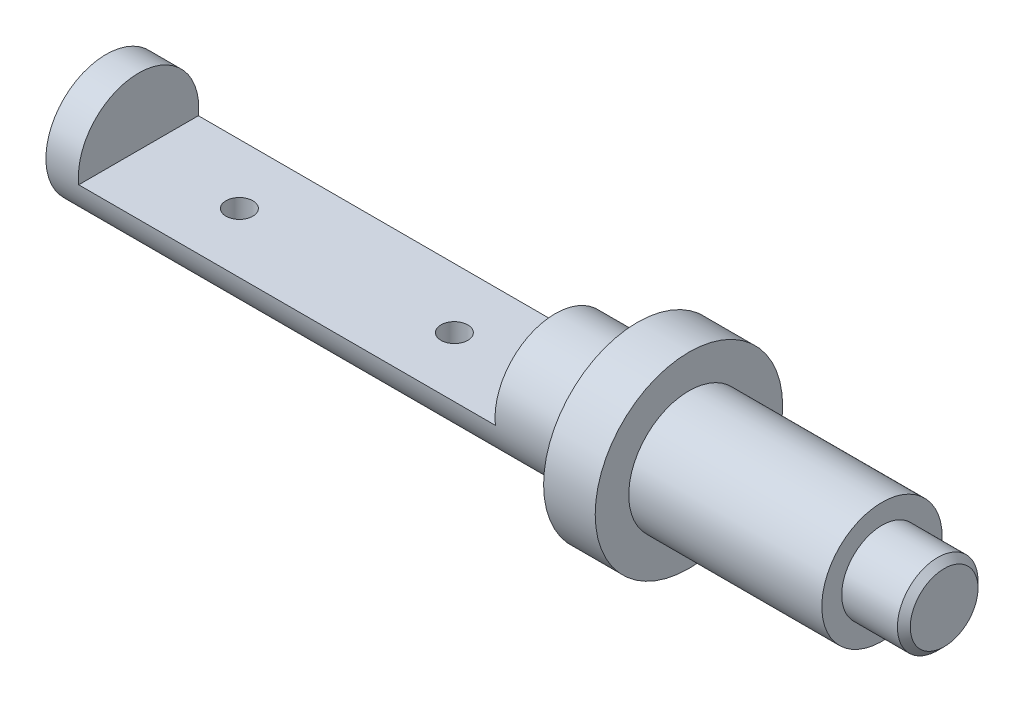
SolidWorks part; units mm, degrees
ref_plane "Front Plane" through (0, 0, 0) normal (0, 0, 1) x (1, 0, 0)
ref_plane "Top Plane" through (0, 0, 0) normal (0, 1, 0) x (1, 0, 0)
ref_plane "Right Plane" through (0, 0, 0) normal (1, 0, 0) x (0, 0, -1)
sketch "Sketch1" plane through (0, 0, 0) normal (1, 0, 0) x (0, 0, -1)
  circle A0 centre (0, 0) radius 28
  dimension "D1" = 56
extrude "Boss-Extrude1" add sketch "Sketch1" along normal blind 247.1
sketch "Sketch2" plane through (247.1, 0, 0) normal (1, 0, 0) x (0, 0, -1)
  circle A0 centre (0, 0) radius 43.6
  dimension "D1" = 87.2
extrude "Boss-Extrude2" add sketch "Sketch2" along normal blind 24
sketch "Sketch3" plane through (271.1, 0, 0) normal (1, 0, 0) x (0, 0, -1)
  circle A0 centre (0, 0) radius 28
  dimension "D1" = 56
extrude "Boss-Extrude3" add sketch "Sketch3" along normal blind 89.8
sketch "Sketch4" plane through (360.9, 0, 0) normal (1, 0, 0) x (0, 0, -1)
  circle A0 centre (0, 0) radius 18.75
  dimension "D1" = 37.5
extrude "Boss-Extrude4" add sketch "Sketch4" along normal blind 28.9
chamfer "Chamfer1" distance 3 angle 45 1 edges at (389.8, 0, -18.75)
sketch "Sketch5" plane through (0, 0, 0) normal (0, 0, 1) x (1, 0, 0)
  line L0 (247.1, 28) -> (0, 28) construction
  line L1 (15.1, 28) -> (208.9, 28)
  line L2 (15.1, 28) -> (15.1, -3.1)
  line L3 (15.1, -3.1) -> (208.9, -3.1)
  line L4 (208.9, 28) -> (208.9, -3.1)
  line L5 (0, 28) -> (0, -28) construction
  dimension "D1" = 193.8
  dimension "D2" = 15.1
  dimension "D3" = 31.1
extrude "Cut-Extrude1" cut sketch "Sketch5" against normal mid plane 108.9
sketch "Sketch6" plane through (0, -3.1, 0) normal (0, 1, 0) x (1, 0, 0)
  line L0 (208.9, 28) -> (208.9, -28) construction
  line L1 (15.1, -28) -> (15.1, 28) construction
  circle A0 centre (62, 0) radius 6.25
  circle A1 centre (162, 0) radius 6.25
  point P4 (0, 0)
  point P7 (0, 0)
  point P10 (15.1, 0)
  point P11 (0, 0)
  dimension "D1" = 12.5
  dimension "D2" = 46.9
  dimension "D3" = 100
extrude "Cut-Extrude2" cut sketch "Sketch6" against normal up to next
